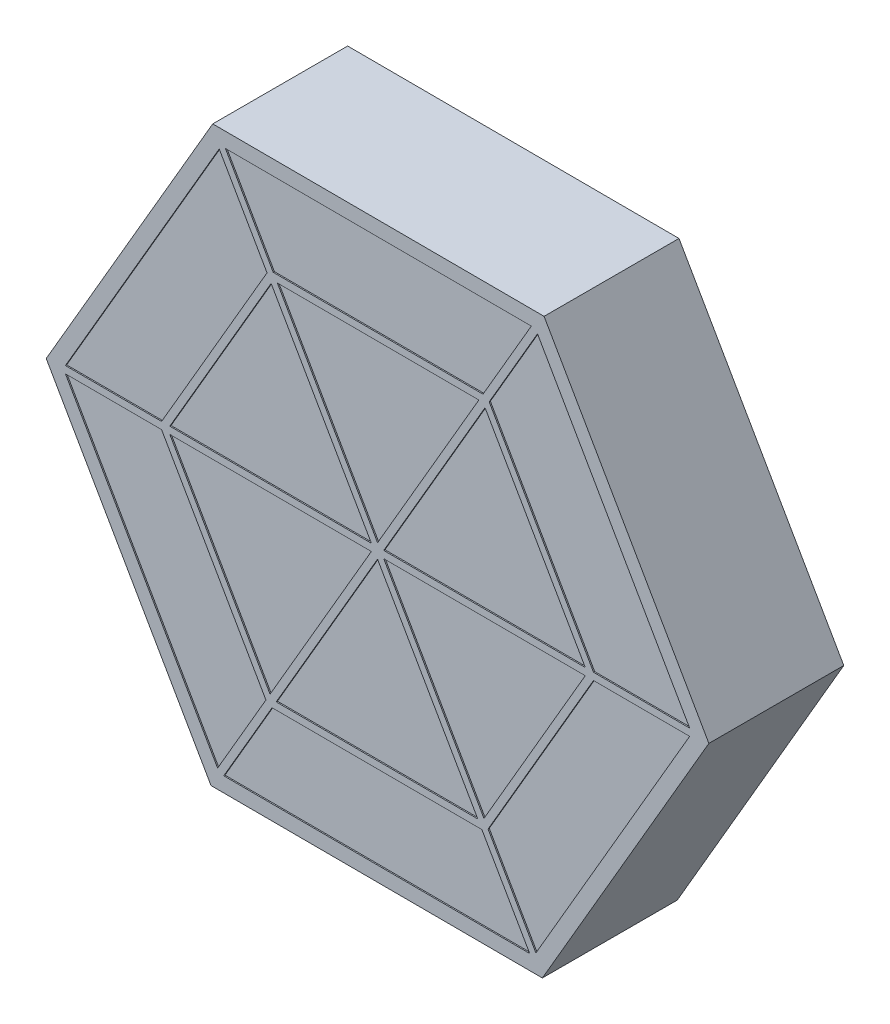
SolidWorks part; units mm, degrees
ref_plane "Alzado" through (0, 0, 0) normal (0, 0, 1) x (1, 0, 0)
ref_plane "Planta" through (0, 0, 0) normal (0, 1, 0) x (1, 0, 0)
ref_plane "Vista lateral" through (0, 0, 0) normal (1, 0, 0) x (0, 0, -1)
sketch "Croquis1" plane through (0, 0, 0) normal (0, 0, 1) x (1, 0, 0)
  line L0 (-53.2339, 92.8183) -> (-55.463, 96.7354)
  line L1 (53.7661, 92.5111) -> (-53.2339, 92.8183)
  line L2 (-53.2339, 92.8183) -> (-107, 0.3072)
  line L3 (-107, 0.3072) -> (-53.7661, -92.5111)
  line L4 (-53.7661, -92.5111) -> (53.2339, -92.8183)
  line L5 (53.2339, -92.8183) -> (107, -0.3072)
  line L6 (107, -0.3072) -> (53.7661, 92.5111)
  line L7 (-55.463, 96.7354) -> (-111.5068, 0.3353)
  line L8 (-111.5068, 0.3353) -> (-56.0438, -96.4001)
  line L9 (-56.0438, -96.4001) -> (55.463, -96.7354)
  line L10 (55.463, -96.7354) -> (111.5068, -0.3353)
  line L11 (111.5068, -0.3353) -> (56.0438, 96.4001)
  line L12 (56.0438, 96.4001) -> (-55.463, 96.7354)
  circle A0 centre (0, 0) radius 92.6651 construction
  circle A1 centre (0, 0) radius 96.5681 construction
  dimension "D1" = 107
  dimension "D2" = 4.5069
extrude "Saliente-Extruir1" add sketch "Croquis1" along normal blind 40
sketch "Croquis2" plane through (0, 0, 40) normal (0, 0, 1) x (1, 0, 0)
  line L1 (111.5068, -0.3353) -> (56.0438, 96.4001)
  line L2 (56.0438, 96.4001) -> (-55.463, 96.7354)
  line L3 (-55.463, 96.7354) -> (-111.5068, 0.3353)
  line L4 (-111.5068, 0.3353) -> (-56.0438, -96.4001)
  line L5 (-56.0438, -96.4001) -> (55.463, -96.7354)
  line L6 (55.463, -96.7354) -> (111.5068, -0.3353)
  circle A0 centre (0, 0) radius 96.5681 construction
extrude "Saliente-Extruir2" add sketch "Croquis2" along normal blind 5
sketch "Croquis4" plane through (0, 0, 45) normal (0, 0, 1) x (1, 0, 0)
  line L86 (-111.5068, 0.3353) -> (111.5068, -0.3353) construction
  line L87 (-111.5104, -0.8647) -> (111.5032, -1.5353)
  line L88 (56.0438, 96.4001) -> (-55.463, 96.7354)
  line L89 (-55.463, 96.7354) -> (-111.5068, 0.3353)
  line L90 (-111.5068, 0.3353) -> (-56.0438, -96.4001)
  line L91 (-56.0438, -96.4001) -> (55.463, -96.7354)
  line L92 (55.463, -96.7354) -> (111.5068, -0.3353)
  line L93 (111.5068, -0.3353) -> (56.0438, 96.4001)
  line L94 (53.142, 91.4088) -> (-52.5913, 91.7267)
  line L95 (-52.5913, 91.7267) -> (-105.7333, 0.3179)
  line L96 (-105.7333, 0.3179) -> (-53.142, -91.4088)
  line L97 (-53.142, -91.4088) -> (52.5913, -91.7267)
  line L98 (52.5913, -91.7267) -> (105.7333, -0.3179)
  line L99 (105.7333, -0.3179) -> (53.142, 91.4088)
  line L100 (73.3733, -0.2206) -> (36.8777, 63.4328)
  line L101 (36.8777, 63.4328) -> (-36.4956, 63.6534)
  line L102 (-36.4956, 63.6534) -> (-73.3733, 0.2206)
  line L103 (-73.3733, 0.2206) -> (-36.8777, -63.4328)
  line L104 (-36.8777, -63.4328) -> (36.4956, -63.6534)
  line L105 (36.4956, -63.6534) -> (73.3733, -0.2206)
  line L106 (70.602, -0.2123) -> (35.4849, 61.037)
  line L107 (35.4849, 61.037) -> (-35.1171, 61.2493)
  line L108 (-35.1171, 61.2493) -> (-70.602, 0.2123)
  line L109 (-70.602, 0.2123) -> (-35.4849, -61.037)
  line L110 (-35.4849, -61.037) -> (35.1171, -61.2493)
  line L111 (35.1171, -61.2493) -> (70.602, -0.2123)
  line L112 (-111.5032, 1.5353) -> (111.5104, 0.8647)
  line L113 (-54.422, 97.3322) -> (56.504, -96.1385)
  line L114 (-56.504, 96.1385) -> (54.422, -97.3322)
  line L115 (57.0812, 95.7969) -> (-55.0064, -97.0032)
  line L116 (55.0064, 97.0032) -> (-57.0812, -95.7969)
  line L117 (111.5032, -1.5353) -> (-111.5104, -0.8647)
  line L118 (111.5104, 0.8647) -> (-111.5032, 1.5353)
  line L119 (54.422, -97.3322) -> (-56.504, 96.1385)
  line L120 (56.504, -96.1385) -> (-54.422, 97.3322)
  line L121 (-57.0812, -95.7969) -> (55.0064, 97.0032)
  line L122 (-55.0064, -97.0032) -> (57.0812, 95.7969)
  circle A18 centre (0, 0) radius 96.5681 construction
  circle A19 centre (0, 0) radius 91.5681 construction
  circle A20 centre (0, 0) radius 63.5434 construction
  circle A21 centre (0, 0) radius 61.1434 construction
  point P55 (0, 0)
  line M44 (55.463, -96.7354) -> (111.5068, -0.3353)
  line M45 (111.5068, -0.3353) -> (56.0438, 96.4001)
  line M46 (56.0438, 96.4001) -> (-55.463, 96.7354)
  line M47 (-55.463, 96.7354) -> (-111.5068, 0.3353)
  line M48 (-111.5068, 0.3353) -> (-56.0438, -96.4001)
  line M49 (-56.0438, -96.4001) -> (55.463, -96.7354)
  dimension "D1" = 2.4
  dimension "D2" = 5
  dimension "D3" = 1.2
  dimension "D4" = 1.2
  dimension "D5" = 6
extrude "Saliente-Extruir3" add sketch "Croquis4" along normal blind 0.4 contours L114 L89 L112 L95 | L112 L89 L87 L96 L95 M48 | L116 L96 L87 M48 | L112 L95 L96 L87 L103 L102 | L114 L95 L94 L113 L88 M47 | L116 L88 L113 L94 | L95 L114 L102 L101 L113 L94 | L116 L94 L99 L115 M46 M45 | L94 L116 L101 L100 L115 L99 | L93 L115 L99 L112 | L112 L100 L105 L87 L98 L99 | L112 L99 L98 L87 M44 M45 | L98 L113 L92 L87 | L96 L116 L90 L115 L97 M49 | L97 L115 L91 L114 | L97 L114 L91 L113 L98 M44 | L104 L114 L97 L98 L113 L105 | L103 L116 L96 L97 L115 L104 | L109 L116 L103 L104 L115 L110 | L110 L115 L104 L114 | L116 L109 L87 L103 | L110 L114 L104 L105 L113 L111 | L87 L115 L114 L110 L111 L113 | L87 L116 L109 L110 L115 L114 | L111 L113 L105 L87 | L112 L106 L111 L87 L105 L100 | L100 L115 L106 L112 | L115 L87 L114 | L114 L116 L87 | L112 L116 L114 L87 L115 L113 | L116 L112 L114 | L113 L116 L112 | L115 L112 L113 | L113 L115 L87 | L112 L115 L113 L87 L111 L106 | L116 L114 L112 L108 L109 L87 | L116 L113 L107 L108 L114 L112 | L107 L116 L113 L112 L115 L106 | L101 L116 L107 L106 L115 L100 | L116 L101 L113 L107 | L102 L114 L108 L107 L113 L101 | L114 L102 L112 L108 | L112 L102 L103 L87 L109 L108
